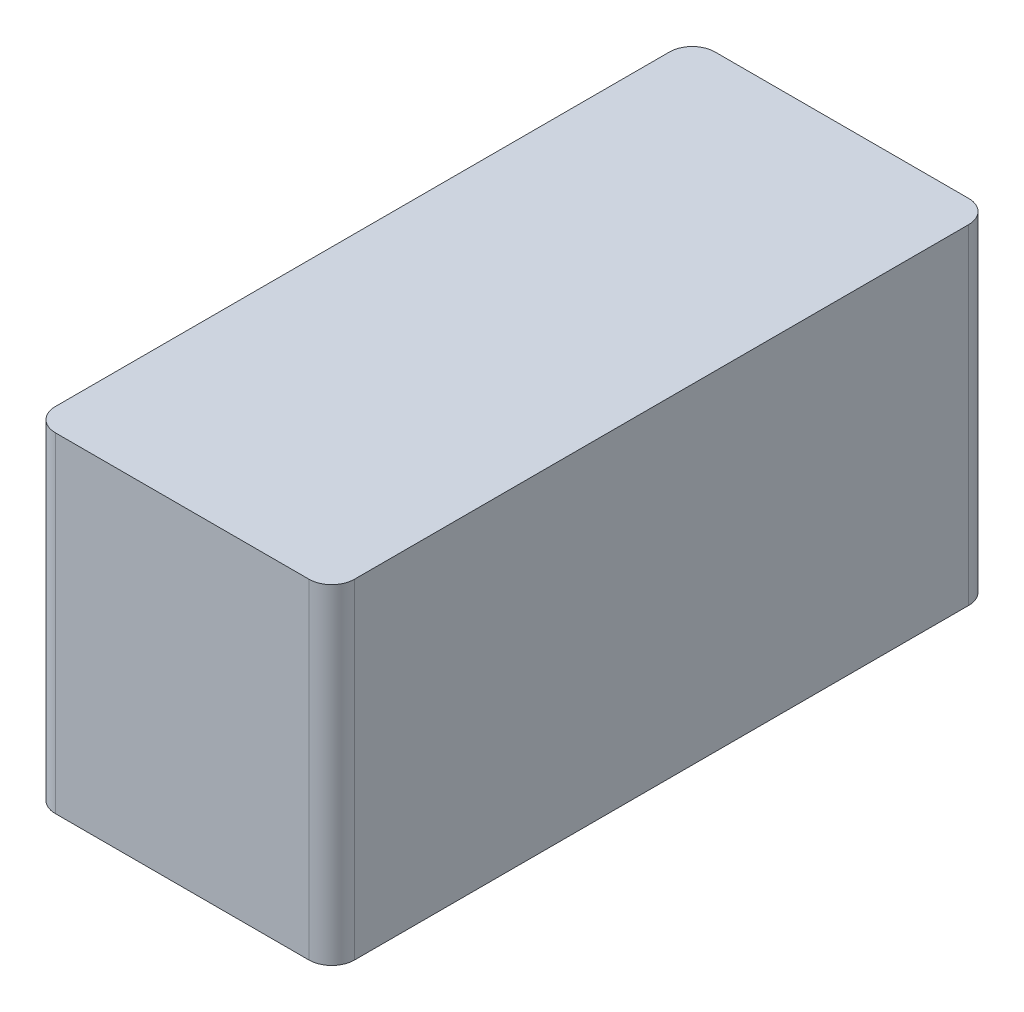
SolidWorks part; units mm, degrees
ref_plane "Front Plane" through (0, 0, 0) normal (0, 0, 1) x (1, 0, 0)
ref_plane "Top Plane" through (0, 0, 0) normal (0, 1, 0) x (1, 0, 0)
ref_plane "Right Plane" through (0, 0, 0) normal (1, 0, 0) x (0, 0, -1)
sketch "Sketch1" plane through (0, 0, 0) normal (0, 1, 0) x (1, 0, 0)
  line L0 (6.575, -14.5) -> (-6.575, -14.5)
  line L1 (6.575, -14.5) -> (6.575, 14.5)
  line L2 (6.575, 14.5) -> (-6.575, 14.5)
  line L3 (-6.575, -14.5) -> (-6.575, 14.5)
  line L4 (6.575, -14.5) -> (-6.575, 14.5) construction
  line L5 (6.575, 14.5) -> (-6.575, -14.5) construction
  point P0 (0, 0)
  dimension "D1" = 13.15
  dimension "D2" = 29
extrude "Boss-Extrude1" add sketch "Sketch1" along normal blind 14.5
fillet "Fillet1" radius 1 4 edges at (-6.575, 7.25, -14.5) (6.575, 7.25, -14.5) (-6.575, 7.25, 14.5) (6.575, 7.25, 14.5)
